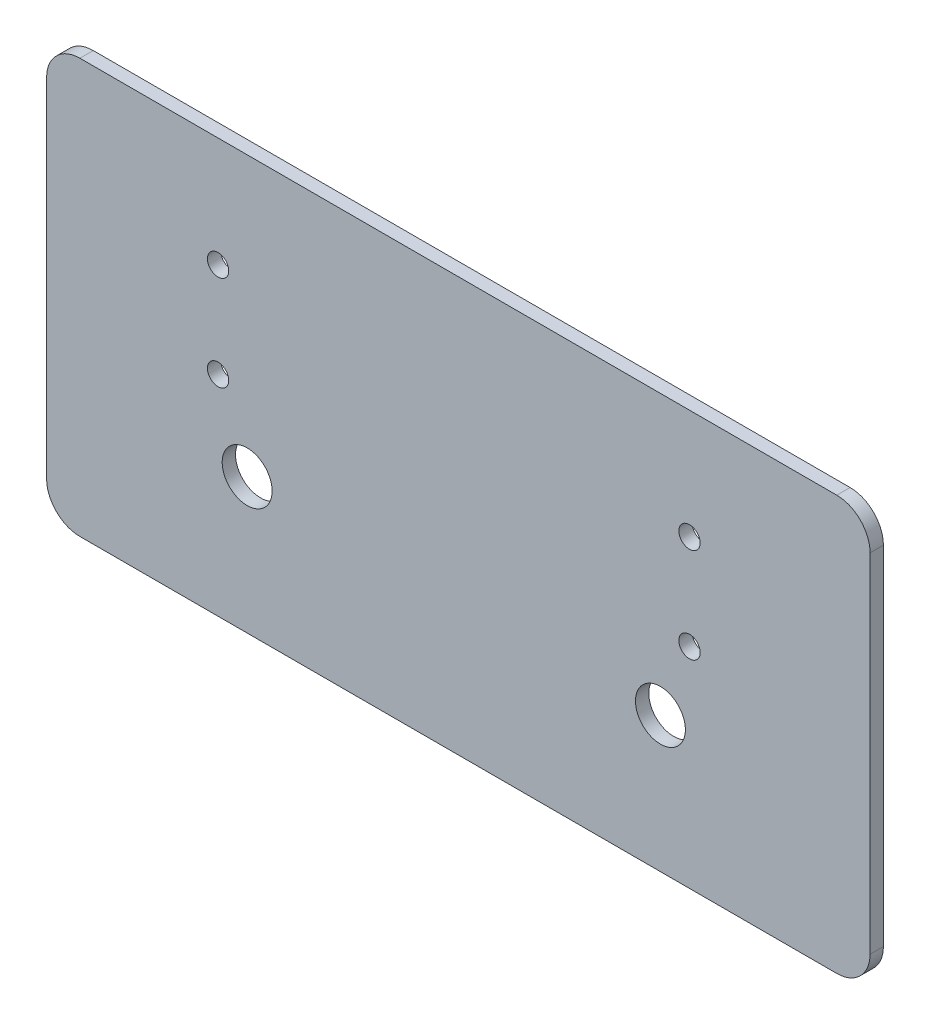
SolidWorks part; units mm, degrees
ref_plane "Front Plane" through (0, 0, 0) normal (0, 0, 1) x (1, 0, 0)
ref_plane "Top Plane" through (0, 0, 0) normal (0, 1, 0) x (1, 0, 0)
ref_plane "Right Plane" through (0, 0, 0) normal (1, 0, 0) x (0, 0, -1)
sketch "Sketch1" plane through (0, 0, 0) normal (0, 0, 1) x (1, 0, 0)
  line L1 (98.3868, -384.8288) -> (-128.911, -384.8288)
  line L2 (108.3868, -374.8288) -> (108.3868, -270.4341)
  line L3 (98.3868, -260.4341) -> (-128.911, -260.4341)
  line L4 (-138.911, -374.8288) -> (-138.911, -270.4341)
  arc A0 (108.3868, -270.4341) -> (98.3868, -260.4341) centre (98.3868, -270.4341) ccw
  arc A1 (-128.911, -260.4341) -> (-138.911, -270.4341) centre (-128.911, -270.4341) ccw
  arc A2 (98.3868, -384.8288) -> (108.3868, -374.8288) centre (98.3868, -374.8288) ccw
  arc A3 (-128.911, -384.8288) -> (-138.911, -374.8288) centre (-128.911, -374.8288) cw
  dimension "D1" = 10
extrude "Boss-Extrude1" add sketch "Sketch1" along normal blind 4
hole_wizard "M6 Clearance Hole1" positions "Sketch4" profile "Sketch2" hole size "M6" standard "ISO" end condition through all
sketch "Sketch4" plane through (0, 0, 4) normal (0, 0, 1) x (1, 0, 0)
  point P0 (54.1627, -293.4157)
  point P3 (54.1627, -321.9157)
  point P6 (45.4264, -344.1655)
  point P9 (-78.681, -344.1655)
  point P12 (-87.4173, -321.9157)
  point P15 (-87.4173, -293.4157)
sketch "Sketch2" plane through (54.1627, -293.4157, 4) normal (1, 0, 0) x (0, -1, 0)
  line L0 (0, 0) -> (0, 4)
  line L1 (0, 4) -> (3.2, 4)
  line L2 (3.2, 4) -> (3.2, 0)
  line L5 (3.2, 0) -> (0, 0)
  line L11 (0, -6.35) -> (0, 107.95) construction
  dimension "Thru Hole Dia." = 6.4
  dimension "Thru Hole Depth" = 4
sketch "Sketch5" plane through (0, 0, 4) normal (0, 0, 1) x (1, 0, 0)
  circle A0 centre (-78.681, -344.1655) radius 7.5
  circle A1 centre (45.4264, -344.1655) radius 7.5
  dimension "D1" = 15
  dimension "D2" = 15
extrude "Cut-Extrude1" cut sketch "Sketch5" against normal blind 40.6781
